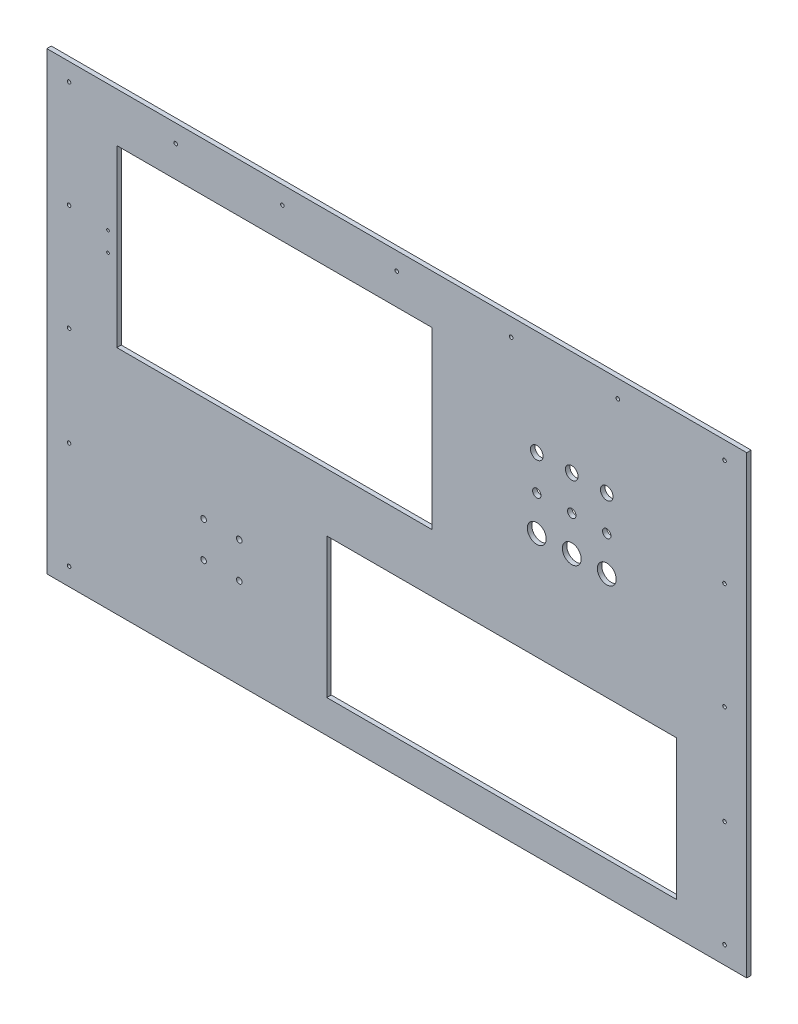
SolidWorks part; units mm, degrees
material "Balsa"
ref_plane "Front Plane" through (0, 0, 0) normal (0, 0, 1) x (1, 0, 0)
ref_plane "Top Plane" through (0, 0, 0) normal (0, 1, 0) x (1, 0, 0)
ref_plane "Right Plane" through (0, 0, 0) normal (1, 0, 0) x (0, 0, -1)
sketch "Sketch1" plane through (0, 0, 0) normal (0, 0, 1) x (1, 0, 0)
  line L0 (500, 270) -> (-500, 270)
  line L1 (-500, -380) -> (500, -380)
  line L2 (-500, -380) -> (-500, 270)
  line L4 (500, -380) -> (500, 270)
  point P0 (0, 0)
  dimension "D1" = 380
  dimension "D2" = 1000
  dimension "D3" = 650
  dimension "D4" = 500
extrude "Boss-Extrude1" add sketch "Sketch1" along normal blind 6.35
sketch "Sketch2" plane through (0, 0, 0) normal (0, 0, 1) x (1, 0, 0)
  line L0 (-500, -380) -> (500, -380) construction
  line L1 (400, -133) -> (-100, -133)
  line L2 (400, -133) -> (400, -333)
  line L3 (400, -333) -> (-100, -333)
  line L4 (-100, -133) -> (-100, -333)
  line L5 (400, -133) -> (-100, -333) construction
  line L6 (400, -333) -> (-100, -133) construction
  line L7 (425, 5) -> (475, 5) construction
  line L8 (425, 5) -> (425, 35) construction
  line L9 (425, 35) -> (475, 35) construction
  line L10 (475, 5) -> (475, 35) construction
  line L11 (425, 5) -> (475, 35) construction
  line L12 (425, 35) -> (475, 5) construction
  line L13 (500, -380) -> (500, 270) construction
  line L14 (258, 55.65) -> (242, 55.65) construction
  line L15 (308, 55.65) -> (292, 55.65) construction
  line L16 (308, 55.65) -> (308, 84.35) construction
  line L17 (308, 84.35) -> (292, 84.35) construction
  line L18 (292, 55.65) -> (292, 84.35) construction
  line L19 (308, 55.65) -> (292, 84.35) construction
  line L20 (308, 84.35) -> (292, 55.65) construction
  line L21 (258, 55.65) -> (258, 84.35) construction
  line L22 (258, 84.35) -> (242, 84.35) construction
  line L23 (242, 55.65) -> (242, 84.35) construction
  line L24 (258, 55.65) -> (242, 84.35) construction
  line L25 (258, 84.35) -> (242, 55.65) construction
  line L26 (208, 55.65) -> (192, 55.65) construction
  line L27 (208, 55.65) -> (208, 84.35) construction
  line L28 (208, 84.35) -> (192, 84.35) construction
  line L29 (192, 55.65) -> (192, 84.35) construction
  line L30 (208, 55.65) -> (192, 84.35) construction
  line L31 (208, 84.35) -> (192, 55.65) construction
  line L32 (-500, 270) -> (-500, -380) construction
  line L33 (-400, 200) -> (50, 200)
  line L34 (-400, 200) -> (-400, -50)
  line L35 (-400, -50) -> (50, -50)
  line L36 (50, 200) -> (50, -50)
  line L37 (-400, 200) -> (50, -50) construction
  line L38 (-400, -50) -> (50, 200) construction
  circle A0 centre (450, -80) radius 3.9688 construction
  circle A1 centre (300, 20) radius 11.5 construction
  circle A2 centre (250, 20) radius 11.5 construction
  circle A3 centre (200, 20) radius 11.5 construction
  circle A4 centre (300, 120) radius 9
  circle A5 centre (250, 120) radius 9
  circle A6 centre (200, 120) radius 9
  circle A7 centre (-225, -251) radius 4
  circle A8 centre (-225, -200) radius 4
  circle A9 centre (-276, -200) radius 4
  circle A10 centre (-276, -251) radius 4
  circle A11 centre (300, -30) radius 8.5 construction
  circle A12 centre (250, -30) radius 8.5 construction
  circle A13 centre (200, -30) radius 8.5 construction
  point P0 (150, -233)
  point P8 (450, 20)
  point P23 (300, 70)
  point P28 (250, 70)
  point P35 (200, 70)
  point P44 (-276, -200)
  point P45 (-225, -200)
  point P46 (-225, -251)
  point P47 (-276, -251)
  point P52 (-175, 75)
  dimension "D5" = 7.9375
  dimension "D14" = 23
  dimension "D24" = 18
  dimension "D25" = 50
  dimension "D34" = 8
  dimension "D35" = 17
  dimension "D1" = 500
  dimension "D2" = 150
  dimension "D3" = 200
  dimension "D4" = 233
  dimension "D6" = 20
  dimension "D7" = 450
  dimension "D8" = 100
  dimension "D9" = 50
  dimension "D10" = 30
  dimension "D11" = 450
  dimension "D12" = 400
  dimension "D13" = 200
  dimension "D15" = 50
  dimension "D16" = 100
  dimension "D17" = 50
  dimension "D18" = 16
  dimension "D19" = 28.7
  dimension "D20" = 28.7
  dimension "D21" = 16
  dimension "D22" = 16
  dimension "D23" = 28.7
  dimension "D26" = 450
  dimension "D27" = 250
  dimension "D28" = 100
  dimension "D29" = 200
  dimension "D30" = 51
  dimension "D31" = 51
  dimension "D32" = 225
  dimension "D36" = 50
extrude "Cut-Extrude1" cut sketch "Sketch2" along normal up to surface (6.35 mm away) up to face at (0, -55, 6.35)
sketch "Sketch3" plane through (0, 0, 0) normal (0, 0, -1) x (-1, 0, 0)
  line L0 (-500, -380) -> (-500, 270) construction
  line L1 (500, -380) -> (-500, -380) construction
  line L2 (-500, 270) -> (500, 270) construction
  line L3 (0, 270) -> (0, -380) construction
  point P0 (-468.25, -354.6)
  point P1 (-468.25, 244.6)
  point P4 (-315.85, 244.6)
  point P5 (-163.45, 244.6)
  point P6 (0, 244.6)
  point P7 (468.25, -202.2)
  point P8 (468.25, -60.2)
  point P9 (-468.25, 92.2)
  point P10 (-468.25, -60.2)
  point P13 (468.25, 92.2)
  point P19 (-468.25, -202.2)
  point P20 (163.45, 244.6)
  point P21 (315.85, 244.6)
  point P22 (468.25, 244.6)
  point P23 (468.25, -354.6)
  dimension "D1" = 31.75
  dimension "D2" = 25.4
  dimension "D3" = 25.4
  dimension "D4" = 152.4
  dimension "D5" = 152.4
  dimension "D6" = 152.4
  dimension "D7" = 152.4
  dimension "D8" = 152.4
hole_wizard "#10 Clearance Hole1 - Mounting Holes" positions "Sketch4" profile "Sketch5" hole size "#10" standard "ANSI Inch" end condition through all
sketch "Sketch4" plane through (0, 0, 0) normal (0, 0, -1) x (-1, 0, 0)
  point P0 (-468.25, -354.6)
  point P3 (-468.25, -202.2)
  point P6 (-468.25, -60.2)
  point P9 (-468.25, 92.2)
  point P12 (-468.25, 244.6)
  point P15 (-315.85, 244.6)
  point P18 (-163.45, 244.6)
  point P21 (0, 244.6)
  point P24 (163.45, 244.6)
  point P27 (315.85, 244.6)
  point P30 (468.25, 244.6)
  point P33 (468.25, 92.2)
  point P36 (468.25, -354.6)
  point P39 (468.25, -202.2)
  point P42 (468.25, -60.2)
sketch "Sketch5" plane through (468.25, -354.6, 0) normal (1, 0, 0) x (0, 1, 0)
  line L0 (0, 0) -> (0, 6.35)
  line L1 (0, 6.35) -> (2.5527, 6.35)
  line L2 (2.5527, 6.35) -> (2.5527, 0)
  line L5 (2.5527, 0) -> (0, 0)
  line L11 (0, -6.35) -> (0, 107.95) construction
  dimension "Thru Hole Dia." = 5.1054
  dimension "Thru Hole Depth" = 6.35
sketch "Sketch6" plane through (0, 0, 0) normal (0, 0, -1) x (-1, 0, 0)
  point P0 (-300, 20)
  point P1 (-250, 20)
  point P3 (-200, 20)
hole_wizard "M27 Clearance Hole1 - Buttons" positions "Sketch7" profile "Sketch8" hole size "M25" standard "ANSI Metric" end condition through all
sketch "Sketch7" plane through (0, 0, 0) normal (0, 0, -1) x (-1, 0, 0)
  point P0 (-300, 20)
  point P3 (-250, 20)
  point P6 (-200, 20)
sketch "Sketch8" plane through (300, 20, 0) normal (1, 0, 0) x (0, 1, 0)
  line L0 (0, 0) -> (0, 6.35)
  line L1 (0, 6.35) -> (13.5, 6.35)
  line L2 (13.5, 6.35) -> (13.5, 0)
  line L5 (13.5, 0) -> (0, 0)
  line L11 (0, -6.35) -> (0, 107.95) construction
  dimension "Thru Hole Dia." = 27
  dimension "Thru Hole Depth" = 6.35
sketch "Sketch9" plane through (0, 0, 0) normal (0, 0, -1) x (-1, 0, 0)
  point P0 (-300, 70)
  point P1 (-250, 70)
  point P3 (-200, 70)
hole_wizard "Ø12.0mm Dowel Hole1 - Switches" positions "Sketch10" profile "Sketch11" hole size "Ø12.0" standard "ANSI Metric" end condition through all
sketch "Sketch10" plane through (0, 0, 0) normal (0, 0, -1) x (-1, 0, 0)
  point P0 (-300, 70)
  point P3 (-250, 70)
  point P6 (-200, 70)
sketch "Sketch11" plane through (300, 70, 0) normal (1, 0, 0) x (0, 1, 0)
  line L0 (0, 0) -> (0, 6.35)
  line L1 (0, 6.35) -> (6, 6.35)
  line L2 (6, 6.35) -> (6, 0)
  line L5 (6, 0) -> (0, 0)
  line L11 (0, -6.35) -> (0, 107.95) construction
  dimension "Thru Hole Dia." = 12
  dimension "Thru Hole Depth" = 6.35
sketch "Sketch14" [suppressed] plane through (0, 0, 0) normal (0, 0, -1) x (-1, 0, 0)
  point P0 (417.0815, 5.15)
  point P1 (388.6335, 17.85)
  point P3 (417.0815, 68.65)
  point P5 (388.6335, 81.35)
  point P7 (388.6335, 144.85)
  point P9 (417.0815, 132.15)
hole_wizard "#6 Clearance Hole1" [suppressed] positions "Sketch15" profile "Sketch16" hole size "#6" standard "ANSI Inch"
sketch "Sketch15" [suppressed] plane through (0, 0, 0) normal (0, 0, -1) x (-1, 0, 0)
  point P0 (417.0815, 132.15)
  point P3 (417.0815, 68.65)
  point P6 (417.0815, 5.15)
sketch "Sketch16" plane through (-417.0815, 132.15, 0) normal (1, 0, 0) x (0, 1, 0)
  line L0 (0, 0) -> (0, 6.35)
  line L1 (0, 6.35) -> (1.8986, 6.35)
  line L2 (1.8986, 6.35) -> (1.8986, 0)
  line L5 (1.8986, 0) -> (0, 0)
  line L11 (0, -6.35) -> (0, 107.95) construction
  dimension "Thru Hole Dia." = 3.7973
  dimension "Thru Hole Depth" = 6.35
sketch "Sketch17" plane through (0, 0, 0) normal (0, 0, -1) x (-1, 0, 0)
  point P0 (412.5562, 89)
  point P1 (412.5562, 61)
hole_wizard "#6 Clearance Hole2" positions "Sketch18" profile "Sketch19" hole size "#6" standard "ANSI Inch" end condition through all
sketch "Sketch18" plane through (0, 0, 0) normal (0, 0, -1) x (-1, 0, 0)
  point P0 (412.5562, 89)
  point P3 (412.5562, 61)
sketch "Sketch19" plane through (-412.5562, 89, 0) normal (1, 0, 0) x (0, 1, 0)
  line L0 (0, 0) -> (0, 6.35)
  line L1 (0, 6.35) -> (1.8986, 6.35)
  line L2 (1.8986, 6.35) -> (1.8986, 0)
  line L5 (1.8986, 0) -> (0, 0)
  line L11 (0, -6.35) -> (0, 107.95) construction
  dimension "Thru Hole Dia." = 3.7973
  dimension "Thru Hole Depth" = 6.35
